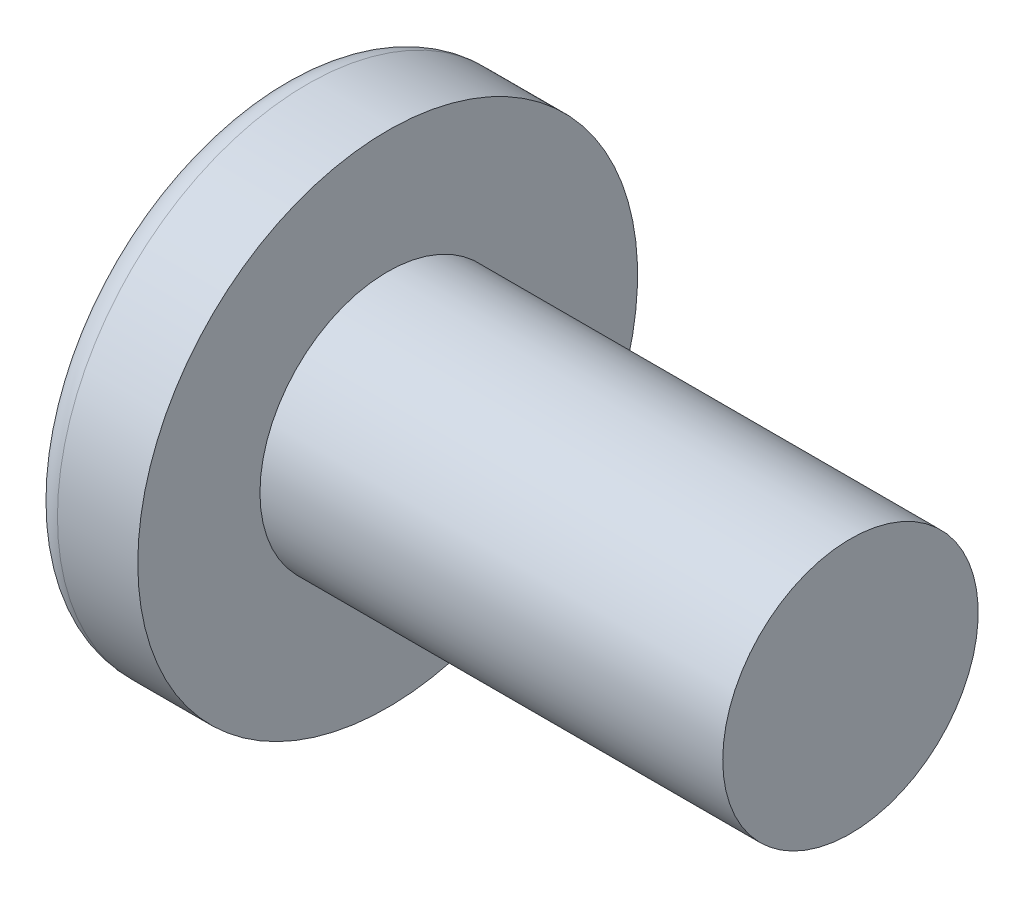
SolidWorks part; units mm, degrees
ref_plane "Plane1" through (0, 0, 0) normal (0, 0, 1) x (1, 0, 0)
ref_plane "Plane2" through (0, 0, 0) normal (0, 1, 0) x (1, 0, 0)
ref_plane "Plane3" through (0, 0, 0) normal (1, 0, 0) x (0, 0, -1)
sketch "BodySke" plane through (0, 0, 0) normal (0, 0, 1) x (1, 0, 0)
  line L0 (2.4638, 1.7526) -> (2.4638, 3.429)
  line L1 (2.86, 6.35) -> (2.86, -3.175) construction
  line L2 (-25.4, 0) -> (127, 0) construction
  line L3 (8.8138, 0) -> (0, 0)
  line L4 (2.4638, 1.7526) -> (8.8138, 1.7526)
  line L5 (8.8138, 1.7526) -> (8.8138, 0)
  line L6 (1.3616, 3.429) -> (2.4638, 3.429)
  line L7 (2.4638, -1.7526) -> (8.8138, -1.7526) construction
  line L8 (2.4638, 6.35) -> (2.4638, -3.175) construction
  arc A0 (1.0521, 3.2702) -> (0, 0) centre (5.6083, 0) ccw
  arc A2 (1.0521, 3.2702) -> (1.3616, 3.429) centre (1.3616, 3.048) cw
  dimension "Head_fillet_rad" = 0.381
  dimension "Head_crown_rad" = 5.6083
  dimension "Head_ht" = 2.4638
  dimension "Diameter" = 3.5052
  dimension "Length" = 6.35
  dimension "Head_dia" = 6.858
  dimension "Advance" = 0.7925
  dimension "Thread_nom" = 6.35
revolve "Base-Revolve" add sketch "BodySke" angle 360 about L2
cosmetic thread "ThreadCosmetic" [suppressed] parameters "Thread_length"=5.5575, "Thread_minor"=2.5603
sketch "Sketch3" plane through (0, 0, 0) normal (1, 0, 0) x (0, 0, -1)
  line L0 (0.4699, -2.2352) -> (-0.4699, -2.2352)
  line L1 (0.4699, -2.2352) -> (0.4699, 2.2352)
  line L2 (-0.4699, 2.2352) -> (0.4699, 2.2352)
  line L3 (-0.4699, 2.2352) -> (-0.4699, -2.2352)
  dimension "D1" = 2.2352
  dimension "Cross_dia" = 4.4704
  dimension "D2" = 0.4699
  dimension "Cross_width" = 0.9398
ref_plane "Plane4" through (2.4384, 0, 0) normal (1, 0, 0) x (0, 0, -1)
sketch "Sketch4" plane through (2.4384, 0, 0) normal (1, 0, 0) x (0, 0, -1)
  line L0 (0.2349, -0.235) -> (-0.2349, -0.235)
  line L1 (0.2349, -0.235) -> (0.235, 0.2349)
  line L2 (-0.2349, 0.2349) -> (0.235, 0.2349)
  line L3 (-0.2349, 0.2349) -> (-0.2349, -0.235)
  dimension "D1" = 0.4699
  dimension "D2" = 0.4699
  dimension "D3" = 0.2349
  dimension "D4" = 0.2349
loft "Cut-Loft1" cut profiles "Sketch3", "Sketch4"
pattern_circular "CirPattern1" count 2 every 90 about axis through (0, 0, 0) along (1, 0, 0) of "Cut-Loft1"
sketch "ThdSchSke" plane through (0, 0, 0) normal (0, 0, 1) x (1, 0, 0)
  line L0 (3.2563, -1.2802) -> (2.9255, -1.7526)
  line L1 (3.2563, -1.2802) -> (3.5871, -1.7526)
  line L2 (3.5871, -1.7526) -> (3.5871, -2.1908)
  line L3 (-3.175, 0) -> (5.1513, 0) construction
  line L5 (3.5871, -2.1908) -> (2.9255, -2.1908)
  line L6 (2.9255, -2.1908) -> (2.9255, -1.7526)
  dimension "Thread_minor" = 2.5603
  dimension "Diameter" = 3.5052
  dimension "Start" = 3.2563
  dimension "SideAngle" = 55
  dimension "VeeAngle" = 70
  dimension "Overcut" = 4.3815
revolve "ThreadSchematic" [suppressed] cut sketch "ThdSchSke" angle 360 about L3
pattern_linear "ThdSchPat" [suppressed]
equation "\"D1@Sketch3\" = \"Cross_dia@Sketch3\" / 2"
equation "\"D2@Sketch3\" = \"Cross_width@Sketch3\" / 2"
equation "\"D1@Sketch4\" = \"Cross_width@Sketch3\" *.5"
equation "\"D2@Sketch4\" = \"D1@Sketch4\""
equation "\"D3@Sketch4\" = \"D1@Sketch4\" / 2"
equation "\"D4@Sketch4\" = \"D2@Sketch4\" / 2"
equation "\"Thread_length@ThreadCosmetic\" = ((sgn( (\"Length@BodySke\" - \"Advance@BodySke\" ) - \"Thread_nom@BodySke\" )-1)*( (\"Length@BodySke\" - \"Advance@BodySke\" ) - \"Thread_nom@BodySke\" ))/-2+ \"Thread_nom@BodySke\""
equation "\"Thread_minor@ThdSchSke\" = \"Thread_minor@ThreadCosmetic\""
equation "\"Diameter@ThdSchSke\" = \"Diameter@BodySke\""
equation "\"Overcut@ThdSchSke\" = \"Diameter@BodySke\" * 1.25"
equation "\"Start@ThdSchSke\" = \"Head_ht@BodySke\" + \"Length@BodySke\" - \"Thread_length@ThreadCosmetic\"  '---Non-countersunk---"
equation "\"Num_threads@ThdSchPat\" = int( \"Thread_length@ThreadCosmetic\" / \"Advance@BodySke\" + 0.999 )  + 1"
equation "\"Advance@ThdSchPat\" = \"Thread_length@ThreadCosmetic\" /  (\"Num_threads@ThdSchPat\" - 1) 'relax it"
